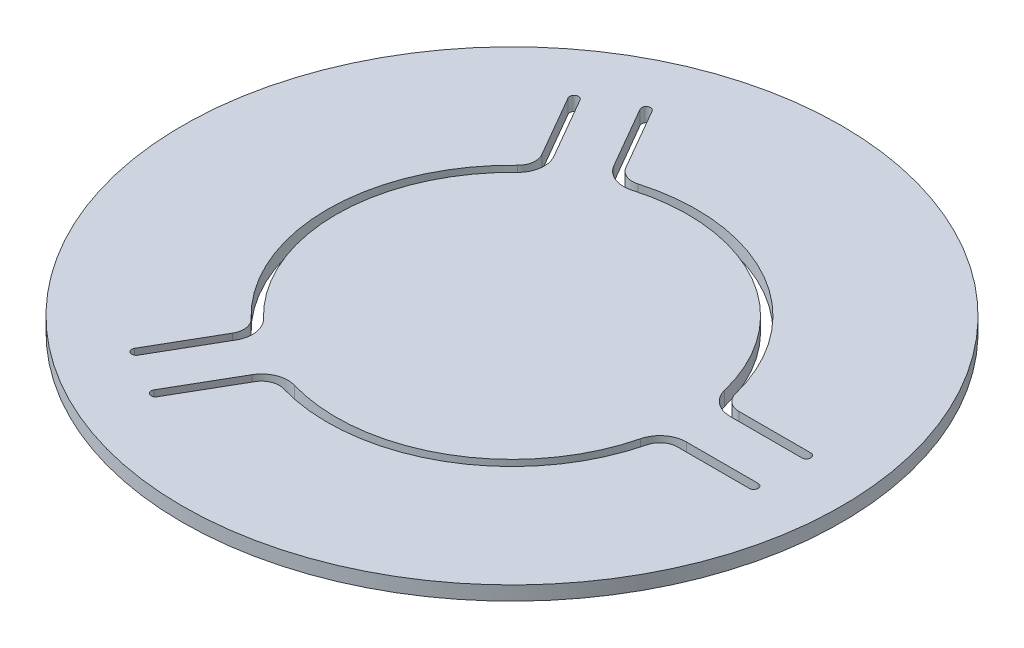
SolidWorks part; units mm, degrees
ref_plane "Front Plane" through (0, 0, 0) normal (0, 0, 1) x (1, 0, 0)
ref_plane "Top Plane" through (0, 0, 0) normal (0, 1, 0) x (1, 0, 0)
ref_plane "Right Plane" through (0, 0, 0) normal (1, 0, 0) x (0, 0, -1)
sketch "Sketch1" plane through (0, 0, 0) normal (0, 1, 0) x (1, 0, 0)
  line L0 (30.5, 3.5) -> (30.5, 2.5) construction
  line L1 (30.5, 2.5) -> (22.3327, 2.5)
  line L2 (10, 17.3205) -> (10.5, 18.1865) construction
  line L3 (22.3327, 3.5) -> (30.5, 3.5)
  line L4 (0, 0) -> (37.5, 0) construction
  line L5 (30.5, -2.5) -> (22.3327, -2.5)
  line L6 (30.5, -3.5) -> (30.5, -2.5) construction
  line L7 (22.3327, -3.5) -> (30.5, -3.5)
  line L8 (-13.0849, -27.6638) -> (-9.0013, -20.5907)
  line L9 (-8.1353, -21.0907) -> (-12.2189, -28.1638)
  line L10 (-17.4151, -25.1638) -> (-13.3314, -18.0907)
  line L11 (-14.1974, -17.5907) -> (-18.2811, -24.6638)
  line L12 (-17.4151, 25.1638) -> (-13.3314, 18.0907)
  line L13 (-14.1974, 17.5907) -> (-18.2811, 24.6638)
  line L14 (-13.0849, 27.6638) -> (-9.0013, 20.5907)
  line L15 (-8.1353, 21.0907) -> (-12.2189, 28.1638)
  circle A0 centre (0, 0) radius 37.5
  arc A1 (19.4197, 4.7826) -> (10, 17.3205) centre (0, 0) ccw
  arc A2 (10.5, 18.1865) -> (20.3907, 5.0217) centre (0, 0) cw
  arc A3 (22.3327, 2.5) -> (19.4197, 4.7826) centre (22.3327, 5.5) cw
  arc A4 (20.3907, 5.0217) -> (22.3327, 3.5) centre (22.3327, 5.5) ccw
  arc A5 (19.4197, -4.7826) -> (10, -17.3205) centre (0, 0) cw
  arc A6 (22.3327, -2.5) -> (19.4197, -4.7826) centre (22.3327, -5.5) ccw
  arc A7 (20.3907, -5.0217) -> (22.3327, -3.5) centre (22.3327, -5.5) cw
  arc A8 (10.5, -18.1865) -> (20.3907, -5.0217) centre (0, 0) ccw
  arc A9 (30.5, 2.5) -> (30.5, 3.5) centre (30.5, 3) ccw
  arc A10 (30.5, -3.5) -> (30.5, -2.5) centre (30.5, -3) ccw
  arc A11 (-5.568, -19.2093) -> (10, -17.3205) centre (0, 0) ccw
  arc A12 (-9.0013, -20.5907) -> (-5.568, -19.2093) centre (-6.4032, -22.0907) cw
  arc A13 (-13.0849, -27.6638) -> (-12.2189, -28.1638) centre (-12.6519, -27.9138) ccw
  arc A14 (-5.8464, -20.1698) -> (-8.1353, -21.0907) centre (-6.4032, -22.0907) ccw
  arc A15 (10.5, -18.1865) -> (-5.8464, -20.1698) centre (0, 0) cw
  arc A16 (-13.8517, -14.4267) -> (-20, 0) centre (0, 0) cw
  arc A17 (-21, 0) -> (-14.5443, -15.148) centre (0, 0) ccw
  arc A18 (-13.3314, -18.0907) -> (-13.8517, -14.4267) centre (-15.9295, -16.5907) ccw
  arc A19 (-14.5443, -15.148) -> (-14.1974, -17.5907) centre (-15.9295, -16.5907) cw
  arc A20 (-18.2811, -24.6638) -> (-17.4151, -25.1638) centre (-17.8481, -24.9138) ccw
  arc A21 (-13.8517, 14.4267) -> (-20, 0) centre (0, 0) ccw
  arc A22 (-13.3314, 18.0907) -> (-13.8517, 14.4267) centre (-15.9295, 16.5907) cw
  arc A23 (-17.4151, 25.1638) -> (-18.2811, 24.6638) centre (-17.8481, 24.9138) ccw
  arc A24 (-14.5443, 15.148) -> (-14.1974, 17.5907) centre (-15.9295, 16.5907) ccw
  arc A25 (-21, 0) -> (-14.5443, 15.148) centre (0, 0) cw
  arc A26 (-5.568, 19.2093) -> (10, 17.3205) centre (0, 0) cw
  arc A27 (10.5, 18.1865) -> (-5.8464, 20.1698) centre (0, 0) ccw
  arc A28 (-9.0013, 20.5907) -> (-5.568, 19.2093) centre (-6.4032, 22.0907) ccw
  arc A29 (-5.8464, 20.1698) -> (-8.1353, 21.0907) centre (-6.4032, 22.0907) cw
  arc A30 (-12.2189, 28.1638) -> (-13.0849, 27.6638) centre (-12.6519, 27.9138) ccw
  point P71 (0, 0)
  dimension "D1" = 75
  dimension "D2" = 60
  dimension "D3" = 1
  dimension "D4" = 2
  dimension "D7" = 20
  dimension "D8" = 3
  dimension "D5" = 5
  dimension "D6" = 7
extrude "Boss-Extrude1" add sketch "Sketch1" along normal mid plane 1.6 contours A0 A30 L15 A29 A27 A2 A4 L3 A9 L1 A3 A1 A26 A28 L14 A8 A15 A14 L9 A13 L8 A12 A11 A5 A6 L5 A10 L7 A7 A17 A25 A24 L13 A23 L12 A22 A21 A16 A18 L10 A20 L11 A19
